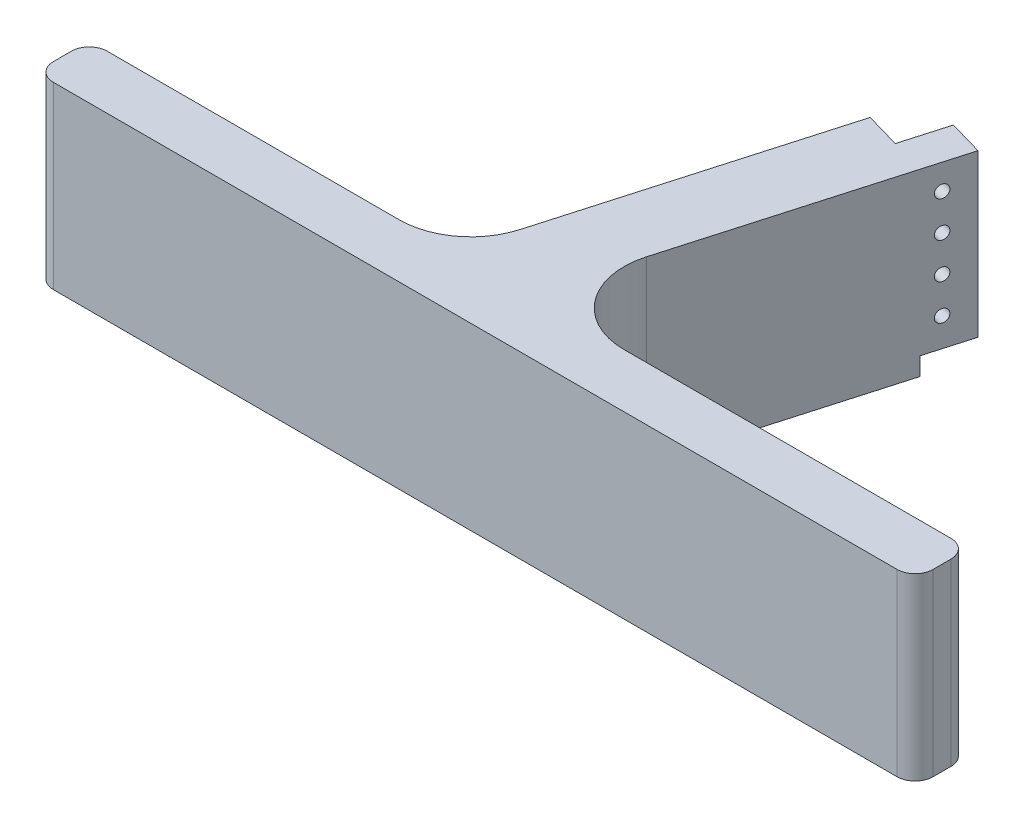
SolidWorks part; units mm, degrees
ref_plane "前视基准面" through (0, 0, 0) normal (0, 0, 1) x (1, 0, 0)
ref_plane "上视基准面" through (0, 0, 0) normal (0, 1, 0) x (1, 0, 0)
ref_plane "右视基准面" through (0, 0, 0) normal (1, 0, 0) x (0, 0, -1)
other "Configuration Table"
sketch "草图1" plane through (0, -21.953, 0) normal (0, -1, 0) x (1, 0, 0)
  line L0 (27.7357, 121.735) -> (18.1226, 118.9805)
  line L1 (18.1226, 118.9805) -> (14.5211, 131.5495)
  line L2 (-21.1412, 218.9805) -> (-122.4607, 218.9805)
  line L3 (-122.4607, 218.9805) -> (-122.4607, 233.9805)
  line L4 (-122.4607, 233.9805) -> (122.4607, 233.9805)
  line L5 (122.4607, 233.9805) -> (122.4607, 218.9805)
  line L6 (122.4607, 218.9805) -> (-0.1284, 218.9805)
  line L7 (-0.1284, 218.9805) -> (27.7357, 121.735)
  line L9 (14.5211, 131.5495) -> (4.7157, 128.7399)
  line L10 (18.2058, 117.9641) -> (14.3289, 131.4944) construction
  line L11 (38.367, 138.3821) -> (-100.0991, 98.707) construction
  line L12 (4.7157, 128.7399) -> (-21.1412, 218.9805)
  arc A1 (-120.7163, 20.5963) -> (48.8356, 112.3019) centre (0, 0) ccw construction
  dimension "D1" = 0.2
  dimension "D2" = 1
  dimension "D3" = 100
  dimension "D4" = 10
  dimension "D5" = 15
extrude "凸台-拉伸1" add sketch "草图1" against normal blind 50
fillet "圆角1" radius 20 2 edges at (-0.1284, 3.047, 218.9805) (-21.1412, 3.047, 218.9805)
fillet "圆角2" radius 5 4 edges at (-122.4607, 3.047, 233.9805) (-122.4607, 3.047, 218.9805) (122.4607, 3.047, 218.9805) (122.4607, 3.047, 233.9805)
sketch "草图2" plane through (57.866, 0, 16.5806) normal (0.9613, 0, 0.2754) x (0.2754, 0, -0.9613)
  circle A0 centre (-117.4607, -9) radius 1.75 construction
  circle A1 centre (-117.4607, 1) radius 1.75 construction
  circle A2 centre (-117.4607, 11) radius 1.75 construction
  circle A3 centre (-117.4607, 21) radius 1.75 construction
  circle A4 centre (-117.4607, -9) radius 1.75
  circle A5 centre (-117.4607, 1) radius 1.75
  circle A6 centre (-117.4607, 11) radius 1.75
  circle A7 centre (-117.4607, 21) radius 1.75
extrude "切除-拉伸1" cut sketch "草图2" against normal up to surface (10 mm away) up to face at (16.3219, 3.047, 125.265)
sketch "草图3" plane through (57.866, 0, 16.5806) normal (0.9613, 0, 0.2754) x (0.2754, 0, -0.9613)
  line L0 (-109.386, -16.953) -> (-122.4607, -16.953)
  line L1 (-109.386, 28.047) -> (-109.386, -21.953) construction
  line L2 (-122.4607, -16.953) -> (-122.4607, -21.953)
  line L3 (-109.386, -21.953) -> (-184.0093, -21.953) construction
  line L4 (-122.4607, -21.953) -> (-109.386, -21.953)
  line L5 (-109.386, -21.953) -> (-109.386, -16.953)
  line L6 (-122.4607, -21.953) -> (-122.4607, -16.953) construction
  line L7 (-104.3246, -16.953) -> (-119.4607, -16.953) construction
  dimension "D1" = 0
  dimension "D2" = 0
extrude "切除-拉伸2" cut sketch "草图3" against normal up to surface (10 mm away) up to face at (15.4164, -9, 128.4252)
